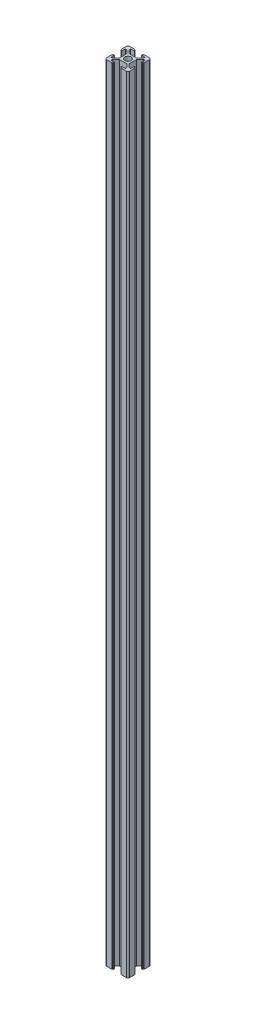
SolidWorks part; units mm, degrees
ref_plane "Front Plane" through (0, 0, 0) normal (0, 0, 1) x (1, 0, 0)
ref_plane "Top Plane" through (0, 0, 0) normal (0, 1, 0) x (1, 0, 0)
ref_plane "Right Plane" through (0, 0, 0) normal (1, 0, 0) x (0, 0, -1)
ref_plane "Plane1" through (0, 0, 0) normal (0, -1, 0) x (1, 0, 0)
sketch "Sketch1" plane through (0, 0, 0) normal (0, -1, 0) x (1, 0, 0)
  line L0 (-8.5, -10) -> (-3.75, -10)
  line L1 (-3.75, -10) -> (-3.75, -9.65)
  line L2 (-3.35, -9.25) -> (-3, -9.25)
  line L3 (-3, -9.25) -> (-3, -8.5)
  line L4 (-3, -8.5) -> (-6.2, -8.5)
  line L5 (-6.2, -8.5) -> (-6.2, -7.2607)
  line L6 (-6.2, -7.2607) -> (-3.2393, -4.3)
  line L7 (-3.2393, -4.3) -> (3.2393, -4.3)
  line L8 (3.2393, -4.3) -> (6.2, -7.2607)
  line L9 (6.2, -7.2607) -> (6.2, -8.5)
  line L10 (6.2, -8.5) -> (3, -8.5)
  line L11 (3, -8.5) -> (3, -9.25)
  line L12 (3, -9.25) -> (3.35, -9.25)
  line L13 (3.75, -9.65) -> (3.75, -10)
  line L14 (3.75, -10) -> (8.5, -10)
  line L15 (10, -8.5) -> (10, -3.75)
  line L16 (10, -3.75) -> (9.65, -3.75)
  line L17 (9.25, -3.35) -> (9.25, -3)
  line L18 (9.25, -3) -> (8.5, -3)
  line L19 (8.5, -3) -> (8.5, -6.2)
  line L20 (8.5, -6.2) -> (7.2607, -6.2)
  line L21 (7.2607, -6.2) -> (4.3, -3.2393)
  line L22 (4.3, -3.2393) -> (4.3, 3.2393)
  line L23 (4.3, 3.2393) -> (7.2607, 6.2)
  line L24 (7.2607, 6.2) -> (8.5, 6.2)
  line L25 (8.5, 6.2) -> (8.5, 3)
  line L26 (8.5, 3) -> (9.25, 3)
  line L27 (9.25, 3) -> (9.25, 3.35)
  line L28 (9.65, 3.75) -> (10, 3.75)
  line L29 (10, 3.75) -> (10, 8.5)
  line L30 (8.5, 10) -> (3.75, 10)
  line L31 (3.75, 10) -> (3.75, 9.65)
  line L32 (3.35, 9.25) -> (3, 9.25)
  line L33 (3, 9.25) -> (3, 8.5)
  line L34 (3, 8.5) -> (6.2, 8.5)
  line L35 (6.2, 8.5) -> (6.2, 7.2607)
  line L36 (6.2, 7.2607) -> (3.2393, 4.3)
  line L37 (3.2393, 4.3) -> (-3.2393, 4.3)
  line L38 (-3.2393, 4.3) -> (-6.2, 7.2607)
  line L39 (-6.2, 7.2607) -> (-6.2, 8.5)
  line L40 (-6.2, 8.5) -> (-3, 8.5)
  line L41 (-3, 8.5) -> (-3, 9.25)
  line L42 (-3, 9.25) -> (-3.35, 9.25)
  line L43 (-3.75, 9.65) -> (-3.75, 10)
  line L44 (-3.75, 10) -> (-8.5, 10)
  line L45 (-10, 8.5) -> (-10, 3.75)
  line L46 (-10, 3.75) -> (-9.65, 3.75)
  line L47 (-9.25, 3.35) -> (-9.25, 3)
  line L48 (-9.25, 3) -> (-8.5, 3)
  line L49 (-8.5, 3) -> (-8.5, 6.2)
  line L50 (-8.5, 6.2) -> (-7.2607, 6.2)
  line L51 (-7.2607, 6.2) -> (-4.3, 3.2393)
  line L52 (-4.3, 3.2393) -> (-4.3, -3.2393)
  line L53 (-4.3, -3.2393) -> (-7.2607, -6.2)
  line L54 (-7.2607, -6.2) -> (-8.5, -6.2)
  line L55 (-8.5, -6.2) -> (-8.5, -3)
  line L56 (-8.5, -3) -> (-9.25, -3)
  line L57 (-9.25, -3) -> (-9.25, -3.35)
  line L58 (-9.65, -3.75) -> (-10, -3.75)
  line L59 (-10, -3.75) -> (-10, -8.5)
  arc A0 (-10, -8.5) -> (-8.5, -10) centre (-8.5, -8.5) ccw
  arc A1 (-3.75, -9.65) -> (-3.35, -9.25) centre (-3.35, -9.65) cw
  arc A2 (3.35, -9.25) -> (3.75, -9.65) centre (3.35, -9.65) cw
  arc A3 (8.5, -10) -> (10, -8.5) centre (8.5, -8.5) ccw
  arc A4 (9.65, -3.75) -> (9.25, -3.35) centre (9.65, -3.35) cw
  arc A5 (9.25, 3.35) -> (9.65, 3.75) centre (9.65, 3.35) cw
  arc A6 (10, 8.5) -> (8.5, 10) centre (8.5, 8.5) ccw
  arc A7 (3.75, 9.65) -> (3.35, 9.25) centre (3.35, 9.65) cw
  arc A8 (-3.35, 9.25) -> (-3.75, 9.65) centre (-3.35, 9.65) cw
  arc A9 (-8.5, 10) -> (-10, 8.5) centre (-8.5, 8.5) ccw
  arc A10 (-9.65, 3.75) -> (-9.25, 3.35) centre (-9.65, 3.35) cw
  arc A11 (-9.25, -3.35) -> (-9.65, -3.75) centre (-9.65, -3.35) cw
  circle A12 centre (0, 0) radius 2.75
extrude "Boss-Extrude1" add sketch "Sketch1" against normal blind 680.25
